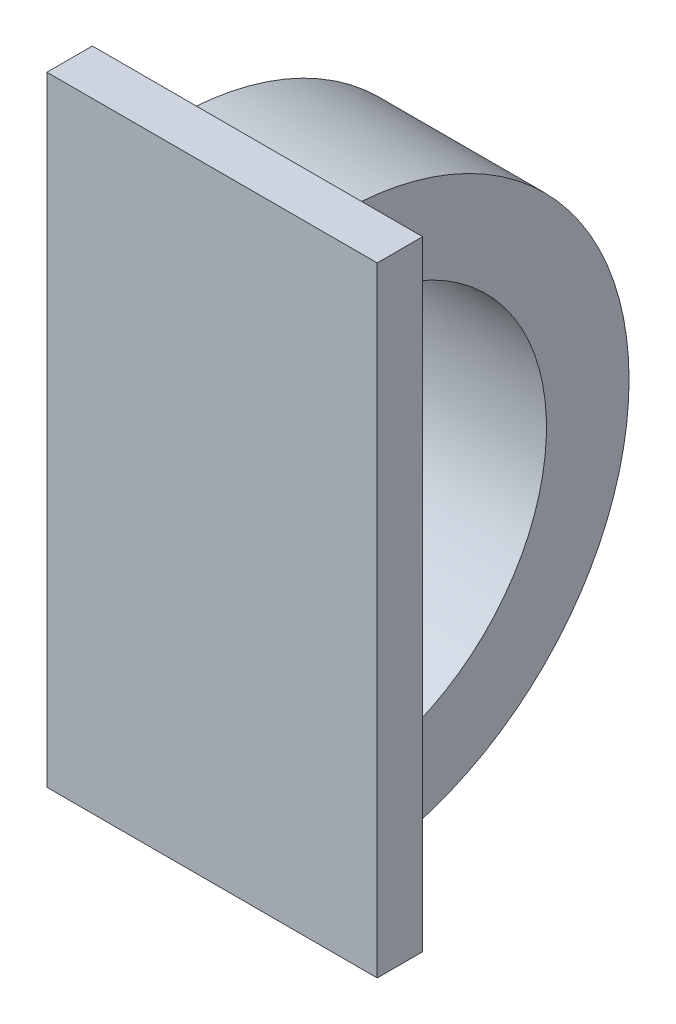
SolidWorks part; units mm, degrees
material "PEI"
ref_plane "Alzado" through (0, 0, 0) normal (0, 0, 1) x (1, 0, 0)
ref_plane "Planta" through (0, 0, 0) normal (0, 1, 0) x (1, 0, 0)
ref_plane "Vista lateral" through (0, 0, 0) normal (1, 0, 0) x (0, 0, -1)
sketch "Croquis1" plane through (0, 0, 0) normal (0, 0, 1) x (1, 0, 0)
  line L1 (-4, 7.5) -> (4, 7.5)
  line L2 (-4, 7.5) -> (-4, -7.5)
  line L3 (-4, -7.5) -> (4, -7.5)
  line L4 (4, 7.5) -> (4, -7.5)
  line L5 (-4, 7.5) -> (4, -7.5) construction
  line L6 (-4, -7.5) -> (4, 7.5) construction
  point P0 (0, 0)
  dimension "D1" = 15
  dimension "D2" = 8
extrude "Saliente-Extruir6" add sketch "Croquis1" along normal blind 1.1
sketch "Croquis8" plane through (0, 0, 0) normal (1, 0, 0) x (0, 0, -1)
  line L0 (0, -7.5) -> (0, 7.5) construction
  line L1 (0, 7) -> (0, 5)
  line L2 (0, -5) -> (0, -7)
  line L3 (0, 7.5) -> (0, -7.5) construction
  arc A0 (0, -5) -> (0, 5) centre (0, 0) ccw
  arc A1 (0, -7) -> (0, 7) centre (0, 0) ccw
  point P1 (5, 0)
  dimension "D1" = 5
  dimension "D2" = 2
extrude "Saliente-Extruir7" add sketch "Croquis8" along normal mid plane 4
